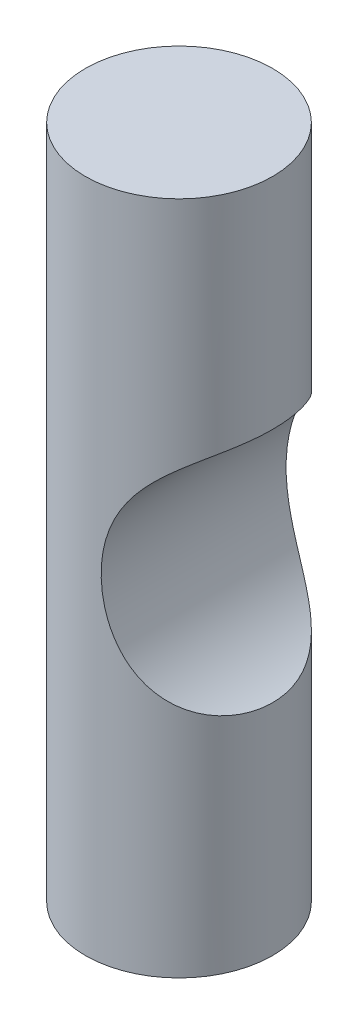
SolidWorks part; units mm, degrees
ref_plane "Front Plane" through (0, 0, 0) normal (0, 0, 1) x (1, 0, 0)
ref_plane "Top Plane" through (0, 0, 0) normal (0, 1, 0) x (1, 0, 0)
ref_plane "Right Plane" through (0, 0, 0) normal (1, 0, 0) x (0, 0, -1)
sketch "Sketch1" plane through (0, 0, 0) normal (0, 1, 0) x (1, 0, 0)
  circle A0 centre (0, 0) radius 4
  dimension "D1" = 8
extrude "Boss-Extrude1" add sketch "Sketch1" along normal blind 28.83
sketch "Sketch2" plane through (0, 0, 0) normal (0, 0, 1) x (1, 0, 0)
  line L0 (0, 28.83) -> (0, 0) construction
  line L1 (4, 28.83) -> (-4, 28.83) construction
  line L2 (0, 14.415) -> (20.511, 14.415) construction
  circle A0 centre (6.1, 14.415) radius 5.475
  dimension "D2" = 10.95
  dimension "D1" = 6.1
extrude "Cut-Extrude1" cut sketch "Sketch2" against normal through all both and the other way through all
sketch "Sketch3" plane through (0, 0, 0) normal (0, -1, 0) x (1, 0, 0)
  circle A0 centre (0, 0.0698) radius 2.5
extrude "Boss-Extrude2" add sketch "Sketch3" along normal blind 1
